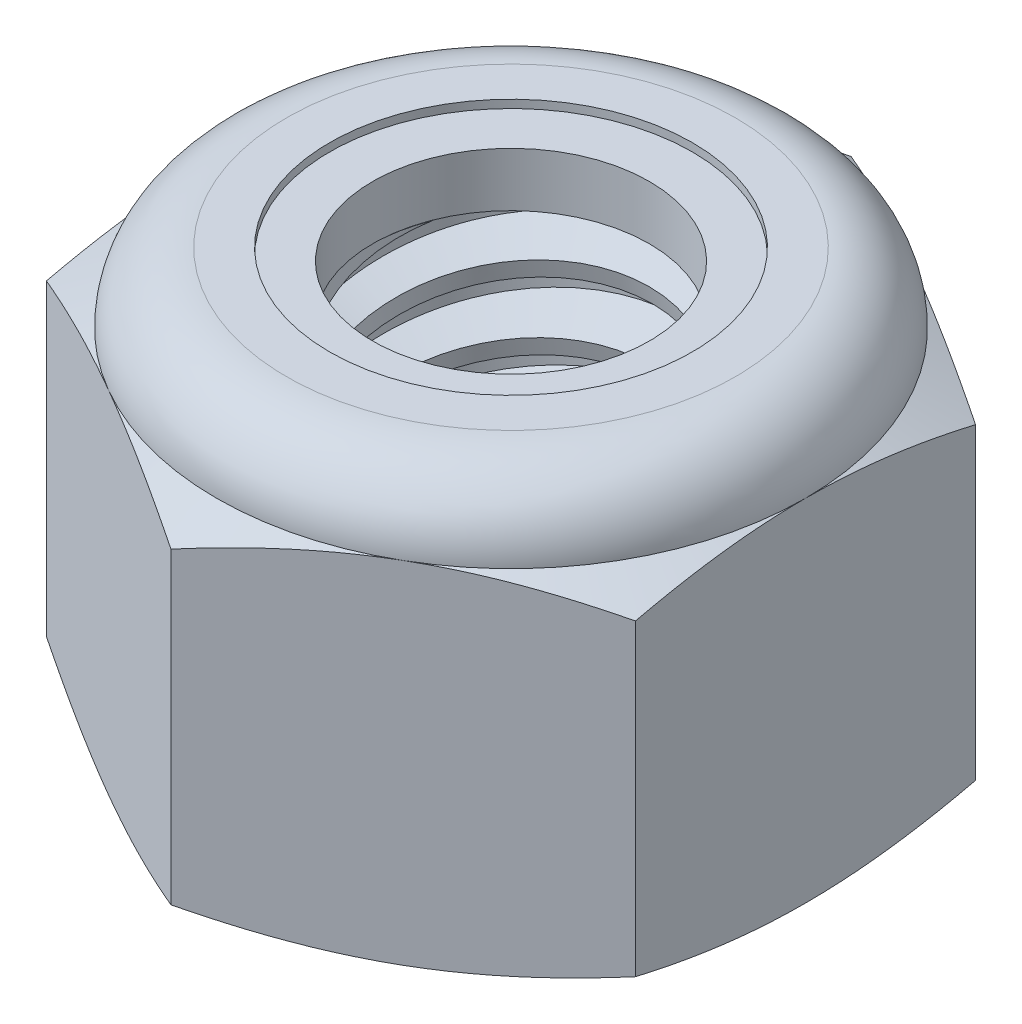
SolidWorks part; units mm, degrees
ref_plane "Front" through (0, 0, 0) normal (0, 0, 1) x (1, 0, 0)
ref_plane "Top" through (0, 0, 0) normal (0, 1, 0) x (1, 0, 0)
ref_plane "Right" through (0, 0, 0) normal (1, 0, 0) x (0, 0, -1)
sketch "Sketch1" plane through (0, 0, 0) normal (0, 1, 0) x (1, 0, 0)
  line L1 (0, 6.4158) -> (-5.5563, 3.2079)
  line L2 (-5.5563, 3.2079) -> (-5.5563, -3.2079)
  line L3 (-5.5563, -3.2079) -> (0, -6.4158)
  line L4 (0, -6.4158) -> (5.5562, -3.2079)
  line L5 (5.5562, -3.2079) -> (5.5562, 3.2079)
  line L6 (5.5562, 3.2079) -> (0, 6.4158)
  circle A0 centre (0, 0) radius 5.5563 construction
  dimension "Hex Flats" = 11.1125
extrude "Extrude1" add sketch "Sketch1" along normal blind 7.9375
sketch "Sketch2" plane through (0, 0, 0) normal (1, 0, 0) x (0, 0, -1)
  line L0 (-3.175, 0) -> (-3.175, 7.9375) construction
  line L1 (0, 0) -> (3.175, 0)
  line L2 (0, 0) -> (0, 7.9375)
  line L3 (0, 7.9375) -> (3.175, 7.9375)
  line L4 (3.175, 0) -> (3.175, 7.9375)
  line L5 (-3.2079, 7.9375) -> (3.2079, 7.9375) construction
  line L7 (0, -3.175) -> (0, 0) construction
  dimension "Thread Dia" = 6.35
revolve "Revolve1" add sketch "Sketch2" angle 360 about L7
sketch "Sketch3" plane through (0, 0, 0) normal (1, 0, 0) x (0, 0, -1)
  line L0 (3.175, 7.9375) -> (-3.175, 7.9375) construction
  line L1 (-3.175, 7.9375) -> (-3.175, 6.6675) construction
  line L2 (-3.175, 6.6675) -> (3.175, 7.9375) construction
  line L3 (3.175, 7.9375) -> (3.2061, 7.7818) construction
  line L4 (3.2061, 7.7818) -> (3.4241, 6.6922)
  line L5 (3.4241, 6.6922) -> (2.6722, 6.9465)
  line L6 (2.6722, 6.9465) -> (2.6099, 7.2579)
  line L7 (2.6099, 7.2579) -> (3.2061, 7.7818)
  line L8 (2.641, 7.1022) -> (3.3151, 7.237) construction
  line L9 (3.175, 7.9375) -> (3.175, 7.209) construction
  line L10 (3.175, 7.209) -> (-3.175, 5.939) construction
  line L11 (-3.175, 5.939) -> (-3.175, 6.6675) construction
  line L12 (-0.2727, 7.9375) -> (0.2727, 5.2105) construction
  line L13 (-3.175, 0) -> (-3.175, 7.9375) construction
  line L14 (0, 7.9375) -> (3.175, 7.9375) construction
  line L15 (3.175, 0) -> (3.175, 7.9375) construction
  point P13 (0, 6.574)
  dimension "D1" = 0.1588
  dimension "D2" = 0.3175
  dimension "Thread Pitch" = 1.27
  dimension "D4" = 60
  dimension "D5" = 1.27
revolve "Cut-Revolve1" cut sketch "Sketch3" angle 360 about L12
pattern_linear "LPattern1" count 6 spacing 1.27 along (0, -1, 0) count 2 spacing 1.27 along (0, 1, 0) of "Cut-Revolve1"
sketch "Sketch4" plane through (0, 0, 0) normal (1, 0, 0) x (0, 0, -1)
  line L0 (0, 7.9375) -> (3.175, 7.9375)
  line L1 (3.175, 7.9375) -> (2.6099, 7.674)
  line L2 (2.6099, 7.674) -> (2.6099, 0.2635)
  line L3 (2.6099, 0.2635) -> (3.175, 0)
  line L4 (3.175, 0) -> (0, 0)
  line L5 (0, 0) -> (0, 7.9375)
  line L6 (3.175, 0) -> (3.175, 7.9375) construction
  line L7 (0, 7.9375) -> (3.175, 7.9375) construction
  line L8 (0, 0) -> (3.175, 0) construction
  line L9 (0, 0) -> (0, 7.9375) construction
  line L10 (0, 7.9375) -> (0, 8.561) construction
  dimension "D1" = 25
revolve "Cut-Revolve2" cut sketch "Sketch4" angle 360 about L10
combine bodies "Combine1" operation type subtract main body 112 bodies to subtract 111
sketch "Sketch5" plane through (0, 0, 0) normal (1, 0, 0) x (0, 0, -1)
  line L0 (0, 0) -> (5.5563, 0)
  line L1 (5.5563, 0) -> (6.4158, 0.4008)
  line L2 (6.4158, 0.4008) -> (6.4158, 6.2138)
  line L3 (6.4158, 6.2138) -> (5.5562, 6.6146)
  line L4 (4.2333, 7.9375) -> (4.2333, 9.2075)
  line L5 (4.2333, 9.2075) -> (7.6858, 9.2075)
  line L6 (7.6858, 9.2075) -> (7.6858, -1.27)
  line L7 (7.6858, -1.27) -> (0, -1.27)
  line L8 (0, -1.27) -> (0, 0)
  line L9 (5.5562, 6.6146) -> (5.5563, 0) construction
  line L10 (0, 0) -> (3.175, 0) construction
  line L13 (6.4158, 3.3073) -> (7.6858, 3.3073) construction
  line L14 (6.4158, 7.9375) -> (6.4158, 0) construction
  line L15 (0, 0) -> (0, 9.2075) construction
  line L20 (0, 9.2075) -> (4.2333, 9.2075) construction
  line L22 (0, 7.9375) -> (3.175, 7.9375) construction
  arc A0 (5.5562, 6.6146) -> (4.2333, 7.9375) centre (4.2333, 6.6146) ccw
  dimension "D1" = 25
  dimension "D2" = 1.27
  dimension "D3" = 7.9375
  dimension "D4" = 1.3229
revolve "Cut-Revolve3" cut sketch "Sketch5" angle 360 about L15
sketch "Sketch6" plane through (0, 0, 0) normal (1, 0, 0) x (0, 0, -1)
  line L0 (0, 6.6146) -> (5.4038, 6.6146)
  line L1 (4.2333, 7.7851) -> (3.4216, 7.7851)
  line L2 (0, 9.2075) -> (0, 6.6146)
  line L3 (3.4216, 9.2075) -> (0, 9.2075)
  line L4 (0, 9.2075) -> (4.2333, 9.2075) construction
  line L5 (0, 0) -> (0, 9.2075) construction
  line L6 (0, 9.2075) -> (0, 44.323) construction
  line L7 (3.4216, 7.7851) -> (3.4216, 9.2075)
  line L8 (4.2333, 7.9375) -> (4.2333, 7.7851) construction
  line L9 (3.4216, 7.7851) -> (2.6099, 7.7851) construction
  line L10 (2.6099, 7.7851) -> (2.6099, 7.674) construction
  arc A0 (5.4038, 6.6146) -> (4.2333, 7.7851) centre (4.2333, 6.6146) ccw
  arc A1 (5.5562, 6.6146) -> (4.2333, 7.9375) centre (4.2333, 6.6146) ccw construction
  dimension "D1" = 0.1524
revolve "Cut-Revolve4" cut sketch "Sketch6" angle 360 about L6
sketch "Sketch7" plane through (0, 0, 0) normal (1, 0, 0) x (0, 0, -1)
  line L0 (2.6099, 6.6908) -> (5.325, 6.6908)
  line L1 (4.2333, 7.7089) -> (2.6099, 7.7089)
  line L2 (2.6099, 7.7089) -> (2.6099, 6.6908)
  line L3 (2.6099, 6.6908) -> (0, 6.6908) construction
  line L4 (0, 6.6908) -> (0, 7.7089) construction
  line L5 (0, 7.7089) -> (2.6099, 7.7089) construction
  line L6 (2.6099, 6.6908) -> (2.6099, 6.6146) construction
  line L7 (0, 6.6146) -> (5.4038, 6.6146) construction
  line L8 (4.2333, 7.7089) -> (4.2333, 7.7851) construction
  arc A0 (5.325, 6.6908) -> (4.2333, 7.7089) centre (4.2333, 6.6146) ccw
  arc A2 (5.4038, 6.6146) -> (4.2333, 7.7851) centre (4.2333, 6.6146) ccw construction
  dimension "D1" = 0.0762
revolve "Revolve2" add sketch "Sketch7" angle 360 about L4
equation "\"D1@Sketch3\"=\"Thread Pitch@Sketch3\"/8"
equation "\"D2@Sketch3\"=\"Thread Pitch@Sketch3\"/4"
equation "\"D5@Sketch3\"=\"Thread Pitch@Sketch3\""
equation "\"D4@LPattern1\"=\"Thread Pitch@Sketch3\""
equation "\"D3@LPattern1\"=\"Thread Pitch@Sketch3\""
equation "\"D1@LPattern1\"=\"Height@Extrude1\"/\"Thread Pitch@Sketch3\""
equation "\"D4@Sketch5\"=\"Height@Extrude1\"/6"
